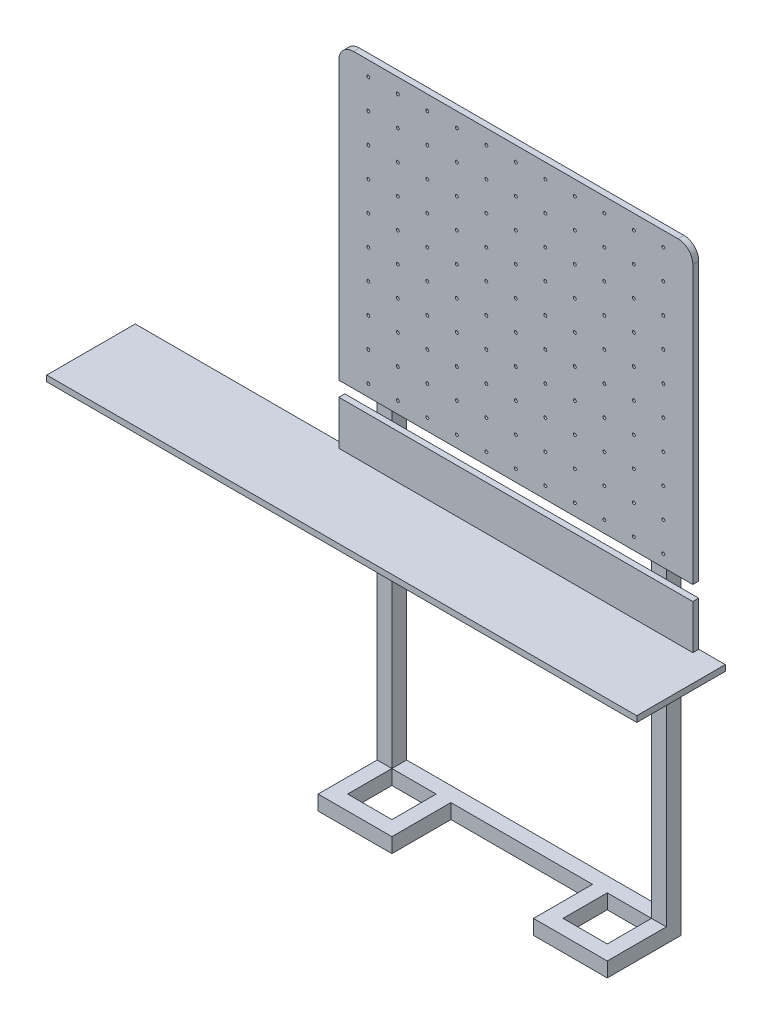
SolidWorks part; units mm, degrees
ref_plane "Alzado" through (0, 0, 0) normal (0, 0, 1) x (1, 0, 0)
ref_plane "Planta" through (0, 0, 0) normal (0, 1, 0) x (1, 0, 0)
ref_plane "Vista lateral" through (0, 0, 0) normal (1, 0, 0) x (0, 0, -1)
sketch "Croquis1" plane through (0, 0, 0) normal (0, 0, 1) x (1, 0, 0)
  line L1 (-600, 495) -> (600, 495)
  line L2 (-600, 495) -> (-600, -495)
  line L3 (-600, -495) -> (600, -495)
  line L4 (600, 495) -> (600, -495)
  line L5 (-600, 495) -> (600, -495) construction
  line L6 (-600, -495) -> (600, 495) construction
  point P0 (0, 0)
  dimension "D1" = 1200
  dimension "D2" = 990
extrude "Saliente-Extruir1" add sketch "Croquis1" along normal blind 20
sketch "Croquis2" plane through (0, 0, 20) normal (0, 0, 1) x (1, 0, 0)
  line L0 (600, 495) -> (-600, 495) construction
  line L1 (-600, 495) -> (-600, -495) construction
  circle A0 centre (-500, 445) radius 5
  circle A1 centre (-400, 445) radius 5
  circle A2 centre (-300, 445) radius 5
  circle A3 centre (-200, 445) radius 5
  circle A4 centre (-100, 445) radius 5
  circle A5 centre (0, 445) radius 5
  circle A6 centre (100, 445) radius 5
  circle A7 centre (200, 445) radius 5
  circle A8 centre (300, 445) radius 5
  circle A9 centre (400, 445) radius 5
  circle A10 centre (500, 445) radius 5
  circle A11 centre (-400, 345) radius 5
  circle A12 centre (-300, 345) radius 5
  circle A13 centre (-200, 345) radius 5
  circle A14 centre (-100, 345) radius 5
  circle A15 centre (0, 345) radius 5
  circle A16 centre (100, 345) radius 5
  circle A17 centre (200, 345) radius 5
  circle A18 centre (300, 345) radius 5
  circle A19 centre (400, 345) radius 5
  circle A20 centre (500, 345) radius 5
  circle A21 centre (-400, 245) radius 5
  circle A22 centre (-300, 245) radius 5
  circle A23 centre (-200, 245) radius 5
  circle A24 centre (-100, 245) radius 5
  circle A25 centre (0, 245) radius 5
  circle A26 centre (100, 245) radius 5
  circle A27 centre (200, 245) radius 5
  circle A28 centre (300, 245) radius 5
  circle A29 centre (400, 245) radius 5
  circle A30 centre (500, 245) radius 5
  circle A31 centre (-400, 145) radius 5
  circle A32 centre (-300, 145) radius 5
  circle A33 centre (-200, 145) radius 5
  circle A34 centre (-100, 145) radius 5
  circle A35 centre (0, 145) radius 5
  circle A36 centre (100, 145) radius 5
  circle A37 centre (200, 145) radius 5
  circle A38 centre (300, 145) radius 5
  circle A39 centre (400, 145) radius 5
  circle A40 centre (500, 145) radius 5
  circle A41 centre (-400, 45) radius 5
  circle A42 centre (-300, 45) radius 5
  circle A43 centre (-200, 45) radius 5
  circle A44 centre (-100, 45) radius 5
  circle A45 centre (0, 45) radius 5
  circle A46 centre (100, 45) radius 5
  circle A47 centre (200, 45) radius 5
  circle A48 centre (300, 45) radius 5
  circle A49 centre (400, 45) radius 5
  circle A50 centre (500, 45) radius 5
  circle A51 centre (-400, -55) radius 5
  circle A52 centre (-300, -55) radius 5
  circle A53 centre (-200, -55) radius 5
  circle A54 centre (-100, -55) radius 5
  circle A55 centre (0, -55) radius 5
  circle A56 centre (100, -55) radius 5
  circle A57 centre (200, -55) radius 5
  circle A58 centre (300, -55) radius 5
  circle A59 centre (400, -55) radius 5
  circle A60 centre (500, -55) radius 5
  circle A61 centre (-400, -155) radius 5
  circle A62 centre (-300, -155) radius 5
  circle A63 centre (-200, -155) radius 5
  circle A64 centre (-100, -155) radius 5
  circle A65 centre (0, -155) radius 5
  circle A66 centre (100, -155) radius 5
  circle A67 centre (200, -155) radius 5
  circle A68 centre (300, -155) radius 5
  circle A69 centre (400, -155) radius 5
  circle A70 centre (500, -155) radius 5
  circle A71 centre (-400, -255) radius 5
  circle A72 centre (-300, -255) radius 5
  circle A73 centre (-200, -255) radius 5
  circle A74 centre (-100, -255) radius 5
  circle A75 centre (0, -255) radius 5
  circle A76 centre (100, -255) radius 5
  circle A77 centre (200, -255) radius 5
  circle A78 centre (300, -255) radius 5
  circle A79 centre (400, -255) radius 5
  circle A80 centre (500, -255) radius 5
  circle A81 centre (-400, -355) radius 5
  circle A82 centre (-300, -355) radius 5
  circle A83 centre (-200, -355) radius 5
  circle A84 centre (-100, -355) radius 5
  circle A85 centre (0, -355) radius 5
  circle A86 centre (100, -355) radius 5
  circle A87 centre (200, -355) radius 5
  circle A88 centre (300, -355) radius 5
  circle A89 centre (400, -355) radius 5
  circle A90 centre (500, -355) radius 5
  circle A91 centre (-400, -455) radius 5
  circle A92 centre (-300, -455) radius 5
  circle A93 centre (-200, -455) radius 5
  circle A94 centre (-100, -455) radius 5
  circle A95 centre (0, -455) radius 5
  circle A96 centre (100, -455) radius 5
  circle A97 centre (200, -455) radius 5
  circle A98 centre (300, -455) radius 5
  circle A99 centre (400, -455) radius 5
  circle A100 centre (500, -455) radius 5
  circle A101 centre (-500, 345) radius 5
  circle A102 centre (-500, 245) radius 5
  circle A103 centre (-500, 145) radius 5
  circle A104 centre (-500, 45) radius 5
  circle A105 centre (-500, -55) radius 5
  circle A106 centre (-500, -155) radius 5
  circle A107 centre (-500, -255) radius 5
  circle A108 centre (-500, -355) radius 5
  circle A109 centre (-500, -455) radius 5
  dimension "D1" = 10
  dimension "D2" = 50
  dimension "D3" = 100
  dimension "D4" = 11
extrude "Cortar-Extruir1" cut sketch "Croquis2" against normal through all
sketch "Croquis3" plane through (0, 0, 0) normal (0, 0, -1) x (-1, 0, 0)
  line L0 (0, 495) -> (0, 0) construction
  line L1 (440, 435) -> (490, 435)
  line L2 (440, 435) -> (440, 385)
  line L3 (440, 385) -> (490, 385)
  line L4 (490, 435) -> (490, 385)
  line L5 (440, 435) -> (490, 385) construction
  line L6 (440, 385) -> (490, 435) construction
  line L7 (-600, 495) -> (600, 495) construction
  line L8 (600, 495) -> (600, -495) construction
  line L9 (-440, 385) -> (-490, 385)
  line L10 (-490, 435) -> (-490, 385)
  line L11 (-440, 435) -> (-490, 435)
  line L12 (-440, 435) -> (-440, 385)
  point P0 (465, 410)
  dimension "D1" = 50
  dimension "D2" = 50
  dimension "D3" = 110
  dimension "D4" = 60
extrude "Saliente-Extruir2" add sketch "Croquis3" along normal blind 50
sketch "Croquis7" plane through (0, 385, 0) normal (0, -1, 0) x (1, 0, 0)
  line L4 (490, 0) -> (440, 0)
  line L5 (440, 0) -> (440, -50)
  line L6 (440, -50) -> (490, -50)
  line L7 (490, -50) -> (490, 0)
  line L8 (490, 0) -> (440, 0)
  line L9 (440, 0) -> (440, -50)
  line L10 (440, -50) -> (490, -50)
  line L11 (490, -50) -> (490, 0)
  line L12 (-440, 0) -> (-490, 0)
  line L13 (-490, 0) -> (-490, -50)
  line L14 (-490, -50) -> (-440, -50)
  line L15 (-440, -50) -> (-440, 0)
  line L16 (-440, 0) -> (-490, 0)
  line L17 (-490, 0) -> (-490, -50)
  line L18 (-490, -50) -> (-440, -50)
  line L19 (-440, -50) -> (-440, 0)
  dimension "D1" = 0
  dimension "D2" = 0
extrude "Saliente-Extruir4" add sketch "Croquis7" along normal blind 2000
sketch "Croquis8" plane through (0, 0, 0) normal (0, 0, 1) x (1, 0, 0)
  line L0 (490, -1615) -> (490, -495) construction
  line L1 (-1310, -695) -> (690, -695)
  line L2 (-1310, -695) -> (-1310, -715)
  line L3 (-1310, -715) -> (690, -715)
  line L4 (690, -695) -> (690, -715)
  line L5 (-1310, -695) -> (690, -715) construction
  line L6 (-1310, -715) -> (690, -695) construction
  line L7 (-600, -495) -> (600, -495) construction
  point P0 (-310, -705)
  dimension "D1" = 2000
  dimension "D2" = 200
  dimension "D3" = 200
  dimension "D4" = 20
extrude "Saliente-Extruir5" add sketch "Croquis8" along normal blind 300
sketch "Croquis9" plane through (0, -695, 0) normal (0, 1, 0) x (1, 0, 0)
  line L0 (-600, -20) -> (-600, 0) construction
  line L1 (600, 0) -> (-600, 0)
  line L2 (600, 0) -> (600, -20)
  line L3 (600, -20) -> (-600, -20)
  line L4 (-600, 0) -> (-600, -20)
  point P5 (-600, -10)
  dimension "D1" = 20
extrude "Saliente-Extruir6" add sketch "Croquis9" along normal blind 150
fillet "Redondeo1" radius 50 2 edges at (600, 495, 10) (-600, 495, 10)
sketch "Croquis10" plane through (440, 0, 0) normal (-1, 0, 0) x (0, 0, 1)
  line L0 (0, -1615) -> (0, -715) construction
  line L1 (-50, -1615) -> (0, -1615)
  line L2 (-50, -1615) -> (-50, -1565)
  line L3 (-50, -1565) -> (0, -1565)
  line L4 (0, -1615) -> (0, -1565)
  dimension "D1" = 50
extrude "Saliente-Extruir7" add sketch "Croquis10" along normal up to next
sketch "Croquis11" plane through (440, 0, 0) normal (-1, 0, 0) x (0, 0, 1)
  line L0 (-50, -1615) -> (-50, 435) construction
  line L1 (0, -495) -> (-50, -495)
  line L2 (0, -495) -> (0, -445)
  line L3 (0, -445) -> (-50, -445)
  line L4 (-50, -495) -> (-50, -445)
  dimension "D1" = 50
extrude "Saliente-Extruir8" add sketch "Croquis11" along normal up to next
sketch "Croquis12" plane through (0, -1615, 0) normal (0, -1, 0) x (1, 0, 0)
  line L0 (0, 0) -> (0, -116.0593) construction
  line L1 (-490, 0) -> (-240, 0)
  line L2 (-490, 0) -> (-490, 200)
  line L3 (-490, 200) -> (-240, 200)
  line L4 (-240, 0) -> (-240, 200)
  line L5 (-440, 150) -> (-290, 150)
  line L6 (-440, 150) -> (-440, 0)
  line L7 (-440, 0) -> (-290, 0)
  line L8 (-290, 150) -> (-290, 0)
  line L9 (440, 0) -> (290, 0)
  line L10 (290, 150) -> (290, 0)
  line L11 (440, 150) -> (290, 150)
  line L12 (440, 150) -> (440, 0)
  line L13 (490, 200) -> (240, 200)
  line L14 (240, 0) -> (240, 200)
  line L15 (490, 0) -> (240, 0)
  line L16 (490, 0) -> (490, 200)
  line M15 (490, 0) -> (-490, 0)
  dimension "D1" = 50
  dimension "D2" = 50
  dimension "D3" = 50
  dimension "D4" = 250
  dimension "D5" = 200
extrude "Saliente-Extruir9" add sketch "Croquis12" against normal blind 50 contours L5 L8 L4 L3 L2 L1 L6 M15 | L16 L13 L14 L10 L11 L12 M15
sketch "Croquis13" plane through (0, 0, 0) normal (0, 0, -1) x (-1, 0, 0)
  line L0 (600, 445) -> (600, -495) construction
  line L1 (600, -315) -> (-340, -315)
  line L2 (600, -315) -> (600, -305)
  line L3 (600, -305) -> (-340, -305)
  line L4 (-340, -315) -> (-340, -305)
  line L5 (600, -495) -> (490, -495) construction
  dimension "D1" = 940
  dimension "D2" = 180
  dimension "D3" = 10
extrude "Saliente-Extruir10" add sketch "Croquis13" along normal blind 10
